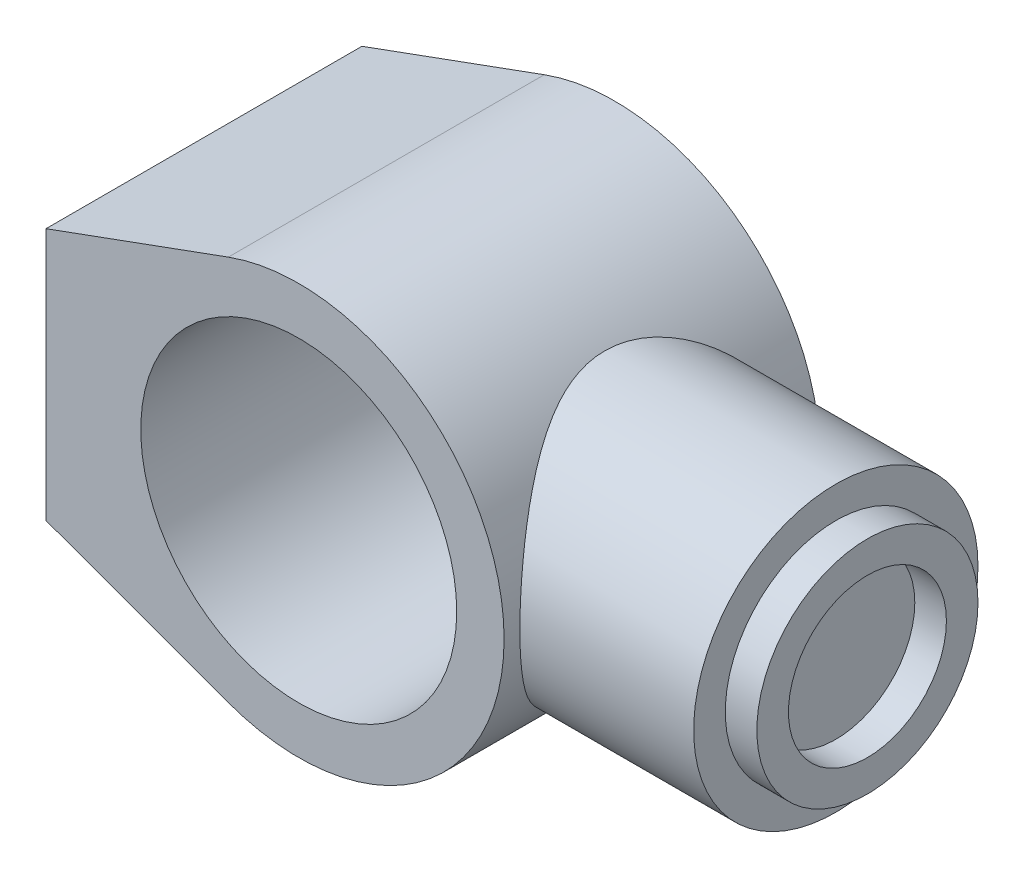
SolidWorks part; units mm, degrees
ref_plane "前视基准面" through (0, 0, 0) normal (0, 0, 1) x (1, 0, 0)
ref_plane "上视基准面" through (0, 0, 0) normal (0, 1, 0) x (1, 0, 0)
ref_plane "右视基准面" through (0, 0, 0) normal (1, 0, 0) x (0, 0, -1)
sketch "草图1" plane through (0, 0, 0) normal (0, 0, 1) x (1, 0, 0)
  line L0 (-80, 40) -> (-80, -40)
  line L1 (-80, 40) -> (-22.2817, 61.0617)
  line L2 (-80, -40) -> (-22.2817, -61.0617)
  arc A0 (-22.2817, -61.0617) -> (-22.2817, 61.0617) centre (0, 0) ccw
  circle A1 centre (0, 0) radius 50
  point P7 (-80, 0)
  dimension "D1" = 130
  dimension "D2" = 100
  dimension "D3" = 80
  dimension "D4" = 80
extrude "凸台-拉伸1" add sketch "草图1" along normal mid plane 100
ref_plane "基准面1" through (120, 0, 0) normal (1, 0, 0) x (0, 0, -1)
sketch "草图2" plane through (120, 0, 0) normal (1, 0, 0) x (0, 0, -1)
  circle A0 centre (0, 0) radius 45
  dimension "D1" = 90
extrude "凸台-拉伸2" add sketch "草图2" against normal up to next
sketch "草图3" plane through (120, 0, 0) normal (1, 0, 0) x (0, 0, -1)
  circle A0 centre (0, 0) radius 35
  circle A1 centre (0, 0) radius 25
  dimension "D1" = 70
  dimension "D2" = 50
extrude "凸台-拉伸3" add sketch "草图3" along normal blind 10
